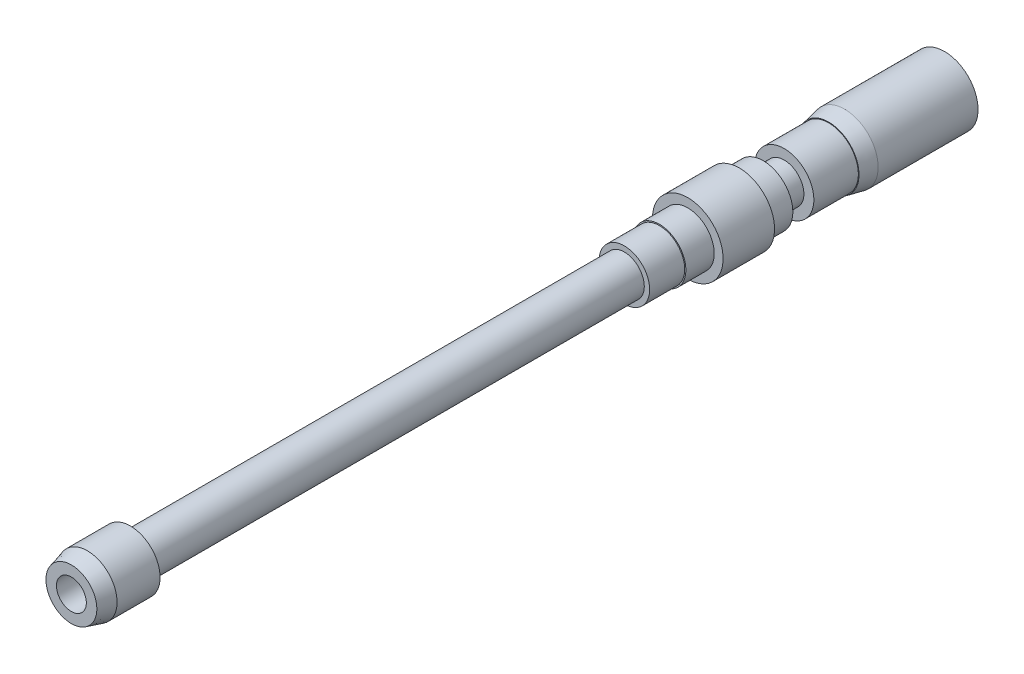
SolidWorks part; units mm, degrees
ref_plane "Front Plane" through (0, 0, 0) normal (0, 0, 1) x (1, 0, 0)
ref_plane "Top Plane" through (0, 0, 0) normal (0, 1, 0) x (1, 0, 0)
ref_plane "Right Plane" through (0, 0, 0) normal (1, 0, 0) x (0, 0, -1)
sketch "Sketch1" plane through (0, 0, 0) normal (0, 0, 1) x (1, 0, 0)
  circle A0 centre (0, 0) radius 4.7371
  dimension "D1" = 9.4742
extrude "Boss-Extrude1" add sketch "Sketch1" against normal blind 9.398
sketch "Sketch2" plane through (0, 0, -9.398) normal (0, 0, -1) x (-1, 0, 0)
  circle A0 centre (0, 0) radius 3.175
  dimension "D1" = 6.35
extrude "Boss-Extrude2" add sketch "Sketch2" along normal blind 78.74
sketch "Sketch3" plane through (0, 0, -88.138) normal (0, 0, -1) x (-1, 0, 0)
  circle A0 centre (0, 0) radius 4.0259
  dimension "D1" = 8.0518
extrude "Boss-Extrude3" add sketch "Sketch3" along normal blind 5.588
sketch "Sketch4" plane through (0, 0, -93.726) normal (0, 0, -1) x (-1, 0, 0)
  circle A0 centre (0, 0) radius 4.2164
  dimension "D1" = 8.4328
extrude "Boss-Extrude4" add sketch "Sketch4" along normal blind 4.5212
sketch "Sketch5" plane through (0, 0, -98.2472) normal (0, 0, -1) x (-1, 0, 0)
  circle A0 centre (0, 0) radius 5.6261
  dimension "D1" = 11.2522
extrude "Boss-Extrude5" add sketch "Sketch5" along normal blind 8.2042
sketch "Sketch6" plane through (0, 0, -106.4514) normal (0, 0, -1) x (-1, 0, 0)
  circle A0 centre (0, 0) radius 4.7244
  dimension "D1" = 9.4488
extrude "Boss-Extrude6" add sketch "Sketch6" along normal blind 3.81
sketch "Sketch7" plane through (0, 0, -110.2614) normal (0, 0, -1) x (-1, 0, 0)
  circle A0 centre (0, 0) radius 3.1369
  dimension "D1" = 6.2738
extrude "Boss-Extrude7" add sketch "Sketch7" along normal blind 3.3528
sketch "Sketch8" plane through (0, 0, -113.6142) normal (0, 0, -1) x (-1, 0, 0)
  circle A0 centre (0, 0) radius 4.7244
  dimension "D1" = 9.4488
extrude "Boss-Extrude8" add sketch "Sketch8" along normal blind 7.0866
sketch "Sketch9" plane through (0, 0, -120.7008) normal (0, 0, -1) x (-1, 0, 0)
  circle A0 centre (0, 0) radius 5.3467
  dimension "D1" = 10.6934
extrude "Boss-Extrude9" add sketch "Sketch9" along normal blind 18.4658
chamfer "Chamfer3" distance 0.508 distance2 2.54 1 edges at (-5.3467, 0, -120.7008)
chamfer "Chamfer4" distance 2.54 angle 15 1 edges at (4.7371, 0, 0)
sketch "Sketch10" plane through (0, 0, 0) normal (0, 0, 1) x (1, 0, 0)
  circle A0 centre (0, 0) radius 2.3813
  dimension "D1" = 4.7625
extrude "Cut-Extrude1" cut sketch "Sketch10" against normal up to surface (139.1666 mm away) up to face at (-5.3467, 0, -139.1666)
